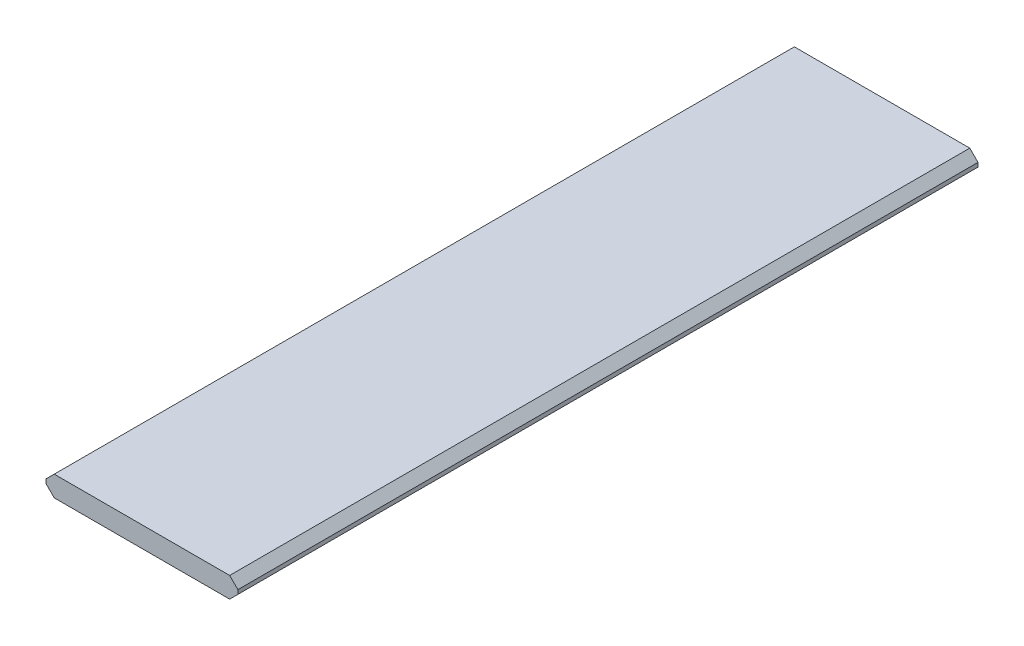
SolidWorks part; units mm, degrees
material "Pine"
ref_plane "Front Plane" through (0, 0, 0) normal (0, 0, 1) x (1, 0, 0)
ref_plane "Top Plane" through (0, 0, 0) normal (0, 1, 0) x (1, 0, 0)
ref_plane "Right Plane" through (0, 0, 0) normal (1, 0, 0) x (0, 0, -1)
sketch "Sketch1" plane through (0, 0, 0) normal (0, 1, 0) x (1, 0, 0)
  line L1 (-88.9, 342.9) -> (88.9, 342.9)
  line L2 (-88.9, 342.9) -> (-88.9, -342.9)
  line L3 (-88.9, -342.9) -> (88.9, -342.9)
  line L4 (88.9, 342.9) -> (88.9, -342.9)
  line L5 (-88.9, 342.9) -> (88.9, -342.9) construction
  line L6 (-88.9, -342.9) -> (88.9, 342.9) construction
  point P0 (0, 0)
  dimension "D1" = 685.8
  dimension "D2" = 177.8
extrude "Boss-Extrude1" add sketch "Sketch1" along normal blind 19.05
chamfer "Chamfer1" distance 7.62 angle 45 4 edges at (-88.9, 19.05, 0) (-88.9, 0, 0) (88.9, 0, 0) (88.9, 19.05, 0)
